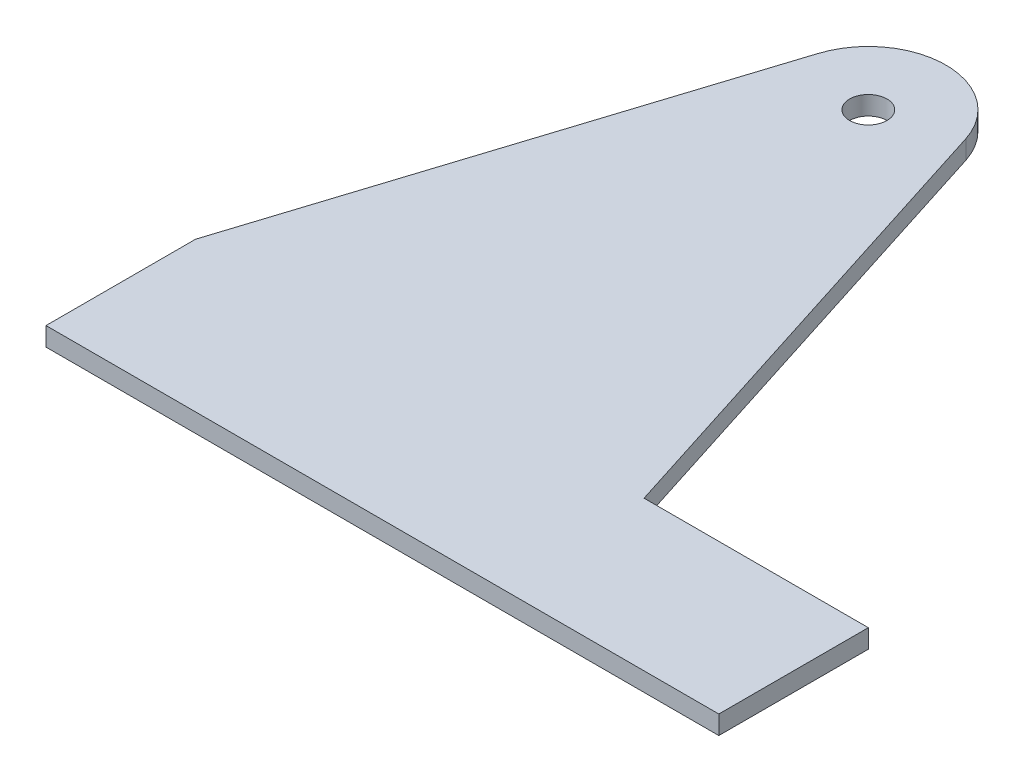
SolidWorks part; units mm, degrees
ref_plane "Front Plane" through (0, 0, 0) normal (0, 0, 1) x (1, 0, 0)
ref_plane "Top Plane" through (0, 0, 0) normal (0, 1, 0) x (1, 0, 0)
ref_plane "Right Plane" through (0, 0, 0) normal (1, 0, 0) x (0, 0, -1)
sketch "Sketch1" plane through (0, 0, 0) normal (0, 1, 0) x (1, 0, 0)
  line L1 (76.2, -152.4) -> (25.107, 7.9976)
  line L2 (-76.2, -152.4) -> (-25.107, 7.9976)
  line L3 (0, 67.2626) -> (0, -107.7613) construction
  line L4 (76.2, -152.4) -> (152.4, -152.4)
  line L5 (152.4, -152.4) -> (152.4, -203.2)
  line L7 (-76.2, -203.2) -> (-76.2, -152.4)
  line L8 (-76.2, -152.4) -> (76.2, -152.4) construction
  line L9 (-76.2, -203.2) -> (152.4, -203.2)
  circle A0 centre (0, 0) radius 6.35
  arc A1 (-25.107, 7.9976) -> (25.107, 7.9976) centre (0, 0) cw
  point P12 (0, -152.4)
  dimension "D3" = 20
  dimension "D4" = 12.7
  dimension "D1" = 228.6
  dimension "D2" = 152.4
  dimension "D5" = 152.4
  dimension "D6" = 50.8
extrude "Boss-Extrude1" add sketch "Sketch1" along normal blind 6.35
